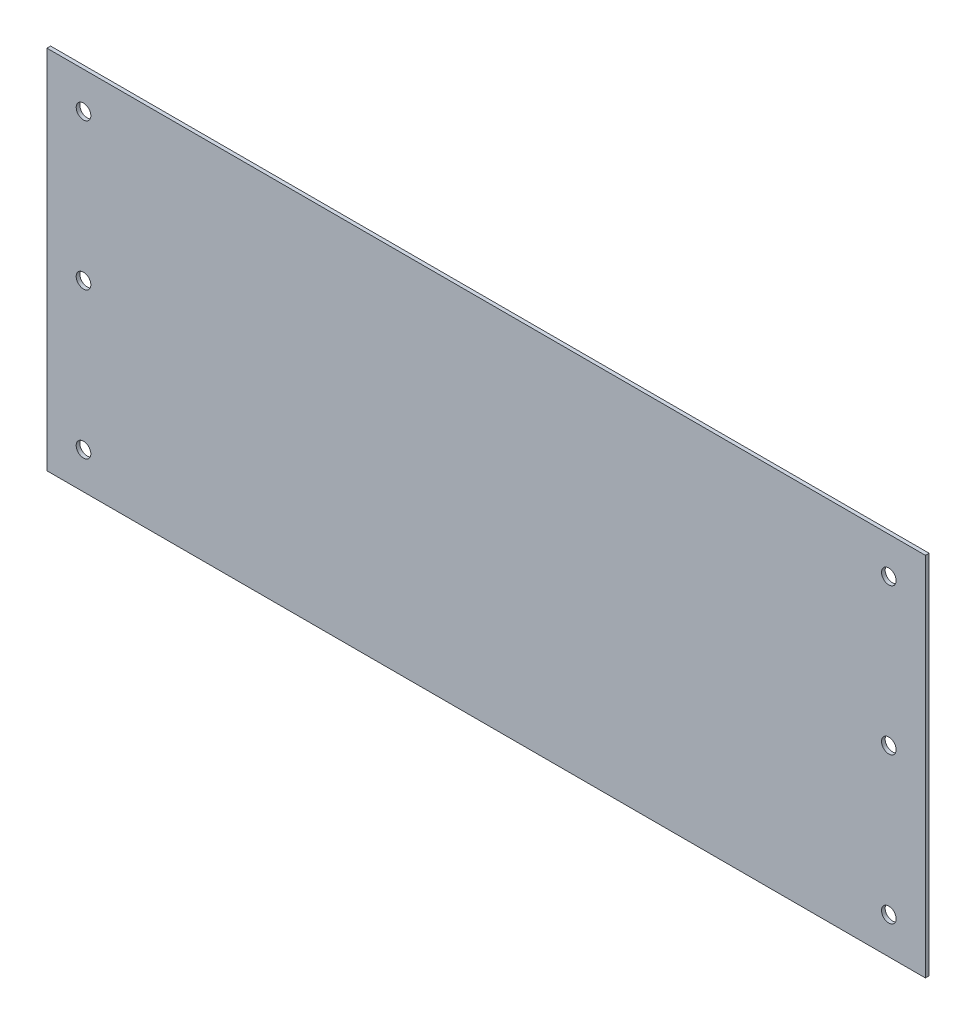
SolidWorks part; units mm, degrees
material "Rubber"
ref_plane "Front Plane" through (0, 0, 0) normal (0, 0, 1) x (1, 0, 0)
ref_plane "Top Plane" through (0, 0, 0) normal (0, 1, 0) x (1, 0, 0)
ref_plane "Right Plane" through (0, 0, 0) normal (1, 0, 0) x (0, 0, -1)
sketch "Sketch1" plane through (0, 0, 0) normal (0, 0, 1) x (1, 0, 0)
  line L1 (-220, 100) -> (20, 100)
  line L2 (-220, 100) -> (-220, 0)
  line L3 (-220, 0) -> (20, 0)
  line L4 (20, 100) -> (20, 0)
extrude "Boss-Extrude1" add sketch "Sketch1" along normal blind 1
sketch "Sketch2" plane through (0, 0, 1) normal (0, 0, 1) x (1, 0, 0)
  circle A0 centre (10, 90) radius 2 construction
  circle A1 centre (10, 50) radius 2 construction
  circle A2 centre (10, 10) radius 2 construction
  circle A3 centre (-210, 10) radius 2 construction
  circle A4 centre (-210, 50) radius 2 construction
  circle A5 centre (-210, 90) radius 2 construction
  circle A6 centre (10, 90) radius 2
  circle A7 centre (10, 50) radius 2
  circle A8 centre (10, 10) radius 2
  circle A9 centre (-210, 10) radius 2
  circle A10 centre (-210, 50) radius 2
  circle A11 centre (-210, 90) radius 2
extrude "Cut-Extrude1" cut sketch "Sketch2" against normal through all
